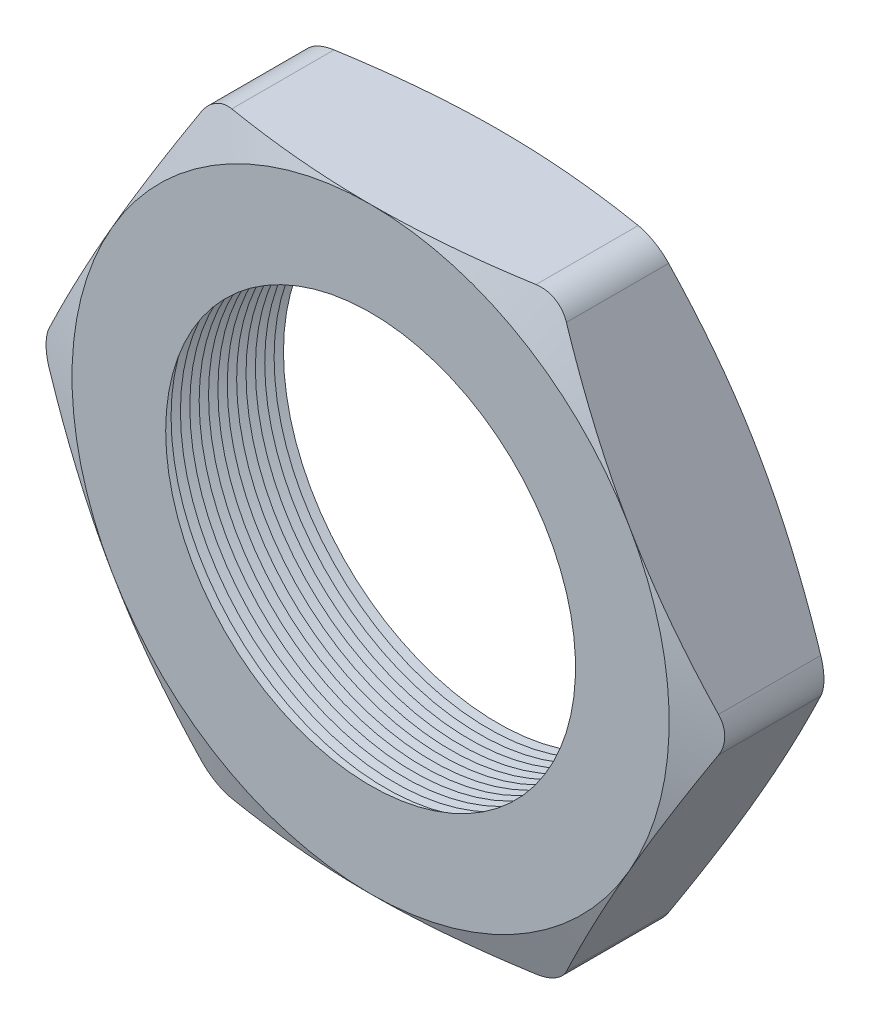
SolidWorks part; units mm, degrees
ref_plane "Front Plane" through (0, 0, 0) normal (0, 0, 1) x (1, 0, 0)
ref_plane "Top Plane" through (0, 0, 0) normal (0, 1, 0) x (1, 0, 0)
ref_plane "Right Plane" through (0, 0, 0) normal (1, 0, 0) x (0, 0, -1)
sketch "Sketch1" plane through (0, 0, 0) normal (0, 0, 1) x (1, 0, 0)
  line L1 (-7.479, 0) -> (-3.7395, -6.477)
  line L2 (-3.7395, -6.477) -> (3.7395, -6.477)
  line L3 (3.7395, -6.477) -> (7.479, 0)
  line L4 (7.479, 0) -> (3.7395, 6.477)
  line L5 (3.7395, 6.477) -> (-3.7395, 6.477)
  line L6 (-3.7395, 6.477) -> (-7.479, 0)
  circle A0 centre (0, 0) radius 6.477 construction
  circle A1 centre (0, 0) radius 4.445
  dimension "TS" = 8.89
  dimension "H" = 12.954
extrude "Extrude1" add sketch "Sketch1" along normal blind 2.794
fillet "Fillet1" radius 0.762 6 edges at (-3.7395, 6.477, 1.397) (-7.479, 0, 1.397) (-3.7395, -6.477, 1.397) (3.7395, -6.477, 1.397) (7.479, 0, 1.397) (3.7395, 6.477, 1.397)
sketch "Sketch2" plane through (0, 0, 2.794) normal (0, 0, 1) x (1, 0, 0)
  line L0 (3.2996, 6.477) -> (-3.2996, 6.477) construction
  circle A0 centre (0, 0) radius 6.477
extrude "Cut-Extrude1" cut sketch "Sketch2" against normal through all draft 70 flip side to cut
sketch "Sketch3" plane through (0, 0, 0) normal (0, 0, -1) x (-1, 0, 0)
  circle A0 centre (0, 0) radius 6.477
extrude "Cut-Extrude2" cut sketch "Sketch3" against normal through all draft 70 flip side to cut
sketch "Sketch4" plane through (0, 0, 0) normal (0, 1, 0) x (1, 0, 0)
  line L0 (-4.445, -2.794) -> (-4.445, -2.3541)
  line L2 (-4.445, -2.3541) -> (-4.826, -2.574)
  line L3 (-4.826, -2.574) -> (-4.445, -2.794)
  line L5 (-4.445, 0) -> (-4.445, -2.794) construction
  line L6 (-4.445, -2.794) -> (4.445, -2.794) construction
  dimension "D1" = 60
  dimension "D2" = 60
  dimension "D3" = 0.381
revolve "Cut-Revolve1" cut sketch "Sketch4" angle 360 about axis through (0, 0, 2.794) along (0, 0, -1)
pattern_linear "LPattern1" count 14 spacing 0.2032 along (0, 0, -1) of "Cut-Revolve1"
